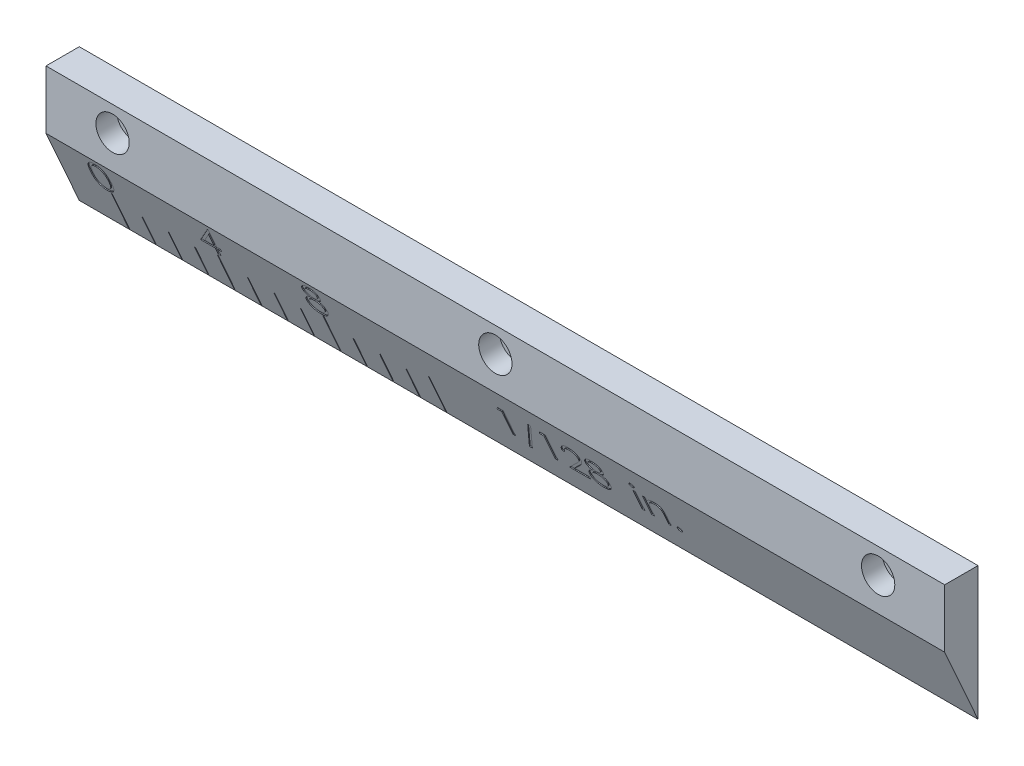
SolidWorks part; units mm, degrees
material "1.4000 (X6Cr13)"
ref_plane "Front Plane" through (0, 0, 0) normal (0, 0, 1) x (1, 0, 0)
ref_plane "Top Plane" through (0, 0, 0) normal (0, 1, 0) x (1, 0, 0)
ref_plane "Right Plane" through (0, 0, 0) normal (1, 0, 0) x (0, 0, -1)
sketch "Sketch1" plane through (0, 0, 0) normal (0, 0, 1) x (1, 0, 0)
  line L1 (-27, -4) -> (27, -4)
  line L2 (-27, -4) -> (-27, 4)
  line L3 (-27, 4) -> (27, 4)
  line L4 (27, -4) -> (27, 4)
  line L5 (-27, -4) -> (27, 4) construction
  line L6 (-27, 4) -> (27, -4) construction
  point P0 (0, 0)
  dimension "D1" = 54
  dimension "D2" = 8
extrude "Boss-Extrude1" add sketch "Sketch1" along normal mid plane 2
sketch "Sketch2" plane through (27, 0, 0) normal (1, 0, 0) x (0, 0, -1)
  line L0 (-1, 0.4921) -> (1, -4)
  line L1 (-1, -4) -> (-1, 4) construction
  line L2 (1, -4) -> (-1, -4)
  line L3 (-1, -4) -> (-1, 0.4921)
  dimension "D1" = 24
extrude "Cut-Extrude1" cut sketch "Sketch2" against normal through all
sketch "Sketch3" plane through (0, 0, 1) normal (0, 0, 1) x (1, 0, 0)
  line L0 (-23, 2.5) -> (23, 2.5) construction
  line L1 (27, 4) -> (-27, 4) construction
  line L2 (27, 0.4921) -> (27, 4) construction
  circle A0 centre (23, 2.5) radius 1
  circle A1 centre (0, 2.5) radius 1
  circle A2 centre (-23, 2.5) radius 1
  point P3 (0, 2.5)
  dimension "D1" = 2
  dimension "D3" = 4
  dimension "D2" = 1.5
extrude "Cut-Extrude2" cut sketch "Sketch3" against normal blind 1.25
sketch "Sketch4" plane through (0, 0, -0.25) normal (0, 0, 1) x (1, 0, 0)
  circle A0 centre (-23, 2.5) radius 0.5
  circle A1 centre (0, 2.5) radius 0.5
  circle A2 centre (23, 2.5) radius 0.5
  dimension "D1" = 1
extrude "Cut-Extrude3" cut sketch "Sketch4" against normal through all
sketch "Sketch5" plane through (0, -0.2902, 0.6517) normal (0, -0.4067, 0.9135) x (1, 0, 0)
  line L0 (-27, -4.0609) -> (27, -4.0609) construction
  line L1 (-24, -1.4309) -> (-23.95, -1.4309)
  line L2 (-24, -1.4309) -> (-24, -4.0109)
  line L3 (-24, -4.0109) -> (-23.95, -4.0109)
  line L4 (-23.95, -1.4309) -> (-23.95, -4.0109)
  line L5 (-22.4125, -2.0109) -> (-22.3625, -2.0109)
  line L6 (-22.4125, -2.0109) -> (-22.4125, -4.0109)
  line L7 (-22.4125, -4.0109) -> (-22.3625, -4.0109)
  line L8 (-22.3625, -2.0109) -> (-22.3625, -4.0109)
  line L9 (-20.825, -2.0109) -> (-20.775, -2.0109)
  line L10 (-20.825, -2.0109) -> (-20.825, -4.0109)
  line L11 (-20.825, -4.0109) -> (-20.775, -4.0109)
  line L12 (-20.775, -2.0109) -> (-20.775, -4.0109)
  line L13 (-19.2375, -2.0109) -> (-19.1875, -2.0109)
  line L14 (-19.2375, -2.0109) -> (-19.2375, -4.0109)
  line L15 (-19.2375, -4.0109) -> (-19.1875, -4.0109)
  line L16 (-19.1875, -2.0109) -> (-19.1875, -4.0109)
  line L17 (-27, -4.0609) -> (-27, 0.8563) construction
  line L18 (-17.65, -1.4309) -> (-17.6, -1.4309)
  line L19 (-17.65, -1.4309) -> (-17.65, -4.0109)
  line L20 (-17.65, -4.0109) -> (-17.6, -4.0109)
  line L21 (-17.6, -1.4309) -> (-17.6, -4.0109)
  line L22 (-16.0625, -2.0109) -> (-16.0125, -2.0109)
  line L23 (-16.0625, -2.0109) -> (-16.0625, -4.0109)
  line L24 (-16.0625, -4.0109) -> (-16.0125, -4.0109)
  line L25 (-16.0125, -2.0109) -> (-16.0125, -4.0109)
  line L26 (-14.475, -2.0109) -> (-14.425, -2.0109)
  line L27 (-14.475, -2.0109) -> (-14.475, -4.0109)
  line L28 (-14.475, -4.0109) -> (-14.425, -4.0109)
  line L29 (-14.425, -2.0109) -> (-14.425, -4.0109)
  line L30 (-12.8875, -2.0109) -> (-12.8375, -2.0109)
  line L31 (-12.8875, -2.0109) -> (-12.8875, -4.0109)
  line L32 (-12.8875, -4.0109) -> (-12.8375, -4.0109)
  line L33 (-12.8375, -2.0109) -> (-12.8375, -4.0109)
  line L34 (-11.3, -1.4309) -> (-11.25, -1.4309)
  line L35 (-11.3, -1.4309) -> (-11.3, -4.0109)
  line L36 (-11.3, -4.0109) -> (-11.25, -4.0109)
  line L37 (-11.25, -1.4309) -> (-11.25, -4.0109)
  line L38 (-9.7125, -2.0109) -> (-9.6625, -2.0109)
  line L39 (-9.7125, -2.0109) -> (-9.7125, -4.0109)
  line L40 (-9.7125, -4.0109) -> (-9.6625, -4.0109)
  line L41 (-9.6625, -2.0109) -> (-9.6625, -4.0109)
  line L42 (-8.125, -2.0109) -> (-8.075, -2.0109)
  line L43 (-8.125, -2.0109) -> (-8.125, -4.0109)
  line L44 (-8.125, -4.0109) -> (-8.075, -4.0109)
  line L45 (-8.075, -2.0109) -> (-8.075, -4.0109)
  line L46 (-6.5375, -2.0109) -> (-6.4875, -2.0109)
  line L47 (-6.5375, -2.0109) -> (-6.5375, -4.0109)
  line L48 (-6.5375, -4.0109) -> (-6.4875, -4.0109)
  line L49 (-6.4875, -2.0109) -> (-6.4875, -4.0109)
  line L51 (-4.95, -1.4309) -> (-4.9, -1.4309)
  line L52 (-4.95, -1.4309) -> (-4.95, -4.0109)
  line L53 (-4.95, -4.0109) -> (-4.9, -4.0109)
  line L54 (-4.9, -1.4309) -> (-4.9, -4.0109)
  dimension "D1" = 2.58
  dimension "D2" = 2
  dimension "D3" = 1.5875
  dimension "D4" = 1.5875
  dimension "D5" = 1.5875
  dimension "D6" = 0.05
  dimension "D7" = 0.05
  dimension "D8" = 3
  dimension "D10" = 6.35
  dimension "D11" = 2.58
  dimension "D12" = 0.05
  dimension "D13" = 1.5875
  dimension "D14" = 0.05
  dimension "D9" = 3
extrude "Cut-Extrude4" cut sketch "Sketch5" against normal blind 0.05
sketch "Sketch6" plane through (0, -0.2902, 0.6517) normal (0, -0.4067, 0.9135) x (1, 0, 0)
  line L0 (-24.8976, -1.3113) -> (-4.8308, -1.3113) construction
  text T0 "0       4       8" font "Century Gothic" height in points 7
extrude "Cut-Extrude5" cut sketch "Sketch6" against normal blind 0.05
sketch "Sketch7" plane through (0, -0.2902, 0.6517) normal (0, -0.4067, 0.9135) x (1, 0, 0)
  line L0 (-1.6007, -2.3625) -> (18.5139, -2.3625) construction
  text T0 " 1/128  in." font "Century Gothic" height in points 7
extrude "Cut-Extrude6" cut sketch "Sketch7" against normal blind 0.05
equation "\"D4@Sketch5\"=\"D3@Sketch5\""
equation "\"D5@Sketch5\"=\"D4@Sketch5\""
